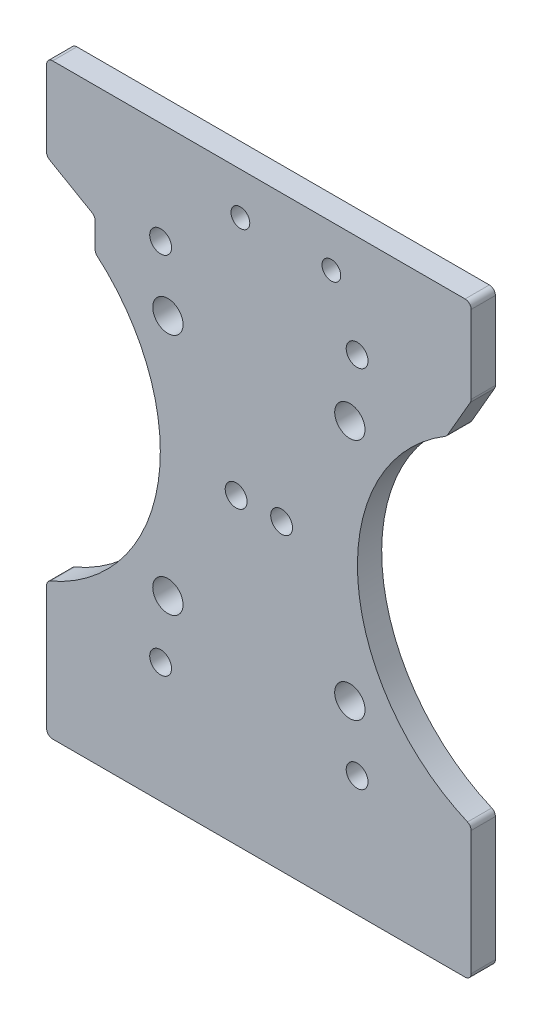
SolidWorks part; units mm, degrees
material "ABS"
ref_plane "前视基准面" through (0, 0, 0) normal (0, 0, 1) x (1, 0, 0)
ref_plane "上视基准面" through (0, 0, 0) normal (0, 1, 0) x (1, 0, 0)
ref_plane "右视基准面" through (0, 0, 0) normal (1, 0, 0) x (0, 0, -1)
other "Configuration Table"
sketch "草图1" plane through (0, 0, 0) normal (0, 0, 1) x (1, 0, 0)
  line L0 (-35, -20) -> (35, -20) construction
  line L1 (-35, -46.9201) -> (35, -46.9201) construction
  line L5 (-35, -46.9201) -> (35, 46.9201) construction
  line L6 (-35, 46.9201) -> (35, -46.9201) construction
  line L7 (-46.25, 0) -> (46.25, 0) construction
  line L8 (-46.25, 0) -> (-16.198, 30.052) construction
  line L9 (-46.25, 0) -> (-16.198, -30.052) construction
  line L10 (0, 46.9201) -> (0, -46.9201) construction
  line L11 (-46.25, 48.25) -> (-46.25, -48.25) construction
  line L12 (-35, 46.9201) -> (-35, 27.8107)
  line L13 (-35, -27.8107) -> (-35, -46.9201)
  line L14 (35, -27.8107) -> (35, -46.9201)
  line L15 (35, 46.9201) -> (35, 27.8107)
  line L16 (-35, 20) -> (35, 20) construction
  line L22 (0, 13.7477) -> (0, -13.7477) construction
  line L23 (0, 13.7477) -> (0, -13.7477) construction
  line L24 (-3.05, 40) -> (11.95, 40) construction
  line L28 (35, 32.8107) -> (30.9582, 25.8101)
  line L29 (-35, 32.8107) -> (-27, 28.1919)
  line L30 (-27, 28.1919) -> (-27, 23.0095)
  line L34 (-35, 46.9201) -> (35, 46.9201)
  line L35 (4.45, 46.9201) -> (4.45, 32.0487) construction
  line L36 (-35, -46.9201) -> (-35, -49.9201)
  line L37 (-35, -49.9201) -> (35, -49.9201)
  line L38 (35, -49.9201) -> (35, -46.9201)
  arc A0 (-46.25, -42.5) -> (-46.25, 42.5) centre (-46.25, 0) ccw construction
  arc A1 (35, 40.984) -> (35, -40.984) centre (46.25, 0) ccw construction
  circle A2 centre (-3.75, 0) radius 1.8
  circle A3 centre (-16.198, 30.052) radius 1.8
  circle A4 centre (-16.198, -30.052) radius 1.8
  circle A5 centre (-16.198, 30.052) radius 1.8
  circle A6 centre (-16.198, -30.052) radius 1.8
  circle A7 centre (16.198, -30.052) radius 1.8
  circle A8 centre (3.75, 0) radius 1.8
  circle A9 centre (16.198, 30.052) radius 1.8
  arc A10 (-35, -27.8107) -> (-35, 27.8107) centre (-46.25, 0) ccw
  arc A11 (35, 27.8107) -> (35, -27.8107) centre (46.25, 0) ccw
  arc A12 (-35, -46.9201) -> (-35, 46.9201) centre (-46.25, 0) ccw construction
  arc A13 (35, 46.9201) -> (35, -46.9201) centre (46.25, 0) ccw construction
  circle A15 centre (0, -20) radius 1.5 construction
  circle A18 centre (-3.05, 40) radius 1.55
  circle A20 centre (11.95, 40) radius 1.55
  circle A21 centre (0, 20) radius 1.5 construction
  point P4 (0, 0)
  dimension "D1" = 85
  dimension "D2" = 45
  dimension "D4" = 3.6
  dimension "D5" = 96.5
  dimension "D6" = 60
  dimension "D9" = 40
  dimension "D10" = 46.25
  dimension "D14" = 15
  dimension "D15" = 3
  dimension "D13" = 3
  dimension "D16" = 30
  dimension "D17" = 5
  dimension "D11" = 40
  dimension "D12" = 4.45
  dimension "D21" = 3.1
  dimension "D3" = 92.5
  dimension "D7" = 70
  dimension "D8" = 40
  dimension "D18" = 5
  dimension "D19" = 60
  dimension "D20" = 8
extrude "凸台-拉伸1" add sketch "草图1" along normal blind 4
sketch "草图3" plane through (0, 0, 0) normal (0, 0, -1) x (-1, 0, 0)
  line L0 (0, 20) -> (0, -49.9201) construction
  line L1 (-3.75, 0) -> (3.75, 0) construction
  line L2 (-15, 20) -> (0, 20) construction
  line L4 (35, -49.9201) -> (-35, -49.9201) construction
  circle A0 centre (-15, 20) radius 2.5
  circle A2 centre (15, 20) radius 2.5
  circle A3 centre (15, -20) radius 2.5
  circle A4 centre (-15, -20) radius 2.5
  dimension "D1" = 20
  dimension "D2" = 5
  dimension "D3" = 15
  dimension "D4" = 7.5
extrude "切除-拉伸2" cut sketch "草图3" against normal blind 10
fillet "圆角1" radius 1 11 edges at (35, -27.8107, 2) (35, -49.9201, 2) (-35, -49.9201, 2) (-35, -27.8107, 2) (-27, 28.1919, 2) (-35, 32.8107, 2) (-27, 23.0095, 2) (30.9582, 25.8101, 2) (35, 32.8107, 2) (-35, 46.9201, 2) (35, 46.9201, 2)
